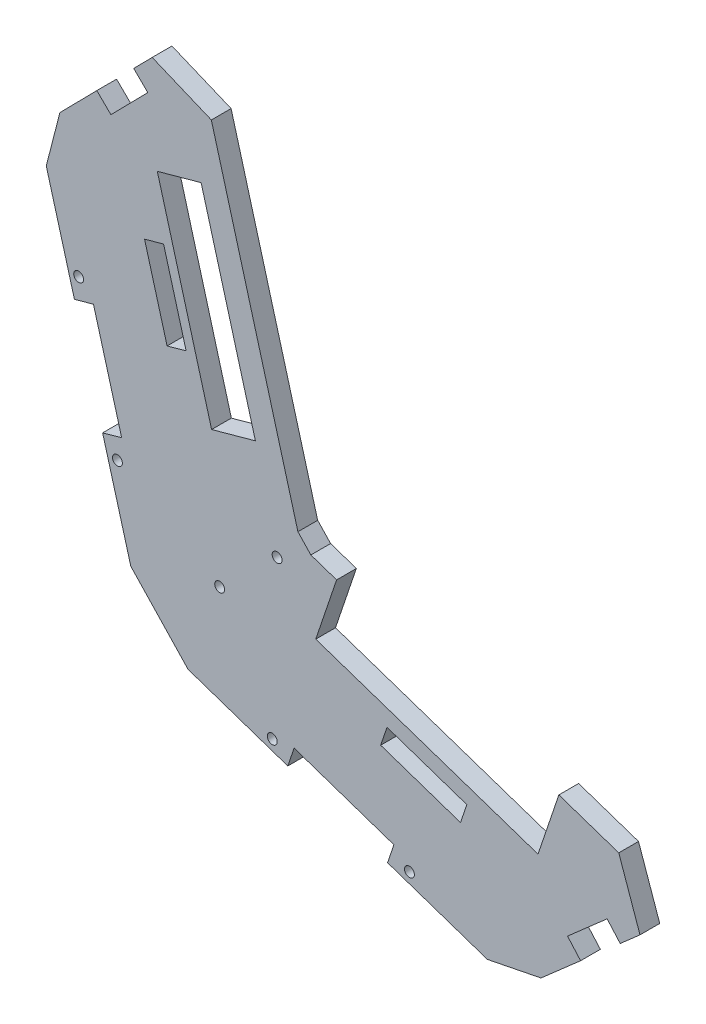
SolidWorks part; units mm, degrees
ref_plane "Alzado" through (0, 0, 0) normal (0, 0, 1) x (1, 0, 0)
ref_plane "Planta" through (0, 0, 0) normal (0, 1, 0) x (1, 0, 0)
ref_plane "Vista lateral" through (0, 0, 0) normal (1, 0, 0) x (0, 0, -1)
sketch "Croquis1" plane through (0, 0, 0) normal (0, 0, 1) x (1, 0, 0)
  line L9 (94.713, -28.6703) -> (124.7846, -2.2941)
  line L10 (124.7846, -2.2941) -> (121.4876, 1.4648)
  line L11 (5.4022, -5.6785) -> (81.1413, -31.3819)
  line L25 (-30.4895, 86.7174) -> (-9.0886, 9.652)
  line L36 (0.9872, 128.6602) -> (-27.0393, 100.1205)
  line L39 (4.5546, 125.1569) -> (0.9872, 128.6602)
  line L40 (-27.0393, 100.1205) -> (-30.4895, 86.7174)
  line L41 (-9.0886, 9.652) -> (5.4022, -5.6785)
  line L42 (81.1413, -31.3819) -> (94.713, -28.6703)
  line L43 (4.5546, 125.1569) -> (29.1628, 36.1106)
  line L44 (29.1628, 36.1106) -> (33.9713, 31.0235)
  line L45 (33.9713, 31.0235) -> (121.4876, 1.4648)
  dimension "D1" = 0.9872
  dimension "D2" = 4.5546
  dimension "D3" = 5.4022
  dimension "D4" = 29.1628
  dimension "D5" = 33.9713
  dimension "D6" = 81.1413
  dimension "D7" = 94.713
  dimension "D8" = 121.4876
  dimension "D9" = 124.7846
  dimension "D10" = 9.0886
  dimension "D11" = 27.0393
  dimension "D12" = 30.4895
  dimension "D13" = 1.4648
  dimension "D14" = 9.652
  dimension "D15" = 31.0235
  dimension "D16" = 36.1106
  dimension "D17" = 86.7174
  dimension "D18" = 100.1205
extrude "Saliente-Extruir1" add sketch "Croquis1" along normal blind 5
sketch "Croquis2" plane through (0, 0, 5) normal (0, 0, 1) x (1, 0, 0)
  line L0 (31.567, 33.5671) -> (-1.8432, 1.9868) construction
  line L1 (33.9713, 31.0235) -> (29.1628, 36.1106) construction
  line L2 (-9.0886, 9.652) -> (5.4022, -5.6785) construction
  circle A0 centre (27.9334, 30.1325) radius 1.25
  circle A1 centre (13.3988, 16.394) radius 1.25
  dimension "D1" = 2.5
  dimension "D2" = 2.5
  dimension "D3" = 20
  dimension "D4" = 5
extrude "Cortar-Extruir1" cut sketch "Croquis2" against normal blind 10
sketch "Croquis3" plane through (0, 0, 0) normal (0, 0, -1) x (-1, 0, 0)
  line L0 (-93.9621, -1.9044) -> (-37.7107, 17.0945)
  line L1 (-121.4876, 1.4648) -> (-33.9713, 31.0235) construction
  line L2 (-93.9621, -1.9044) -> (-97.802, 9.4646)
  line L3 (-37.7107, 17.0945) -> (-41.5506, 28.4636)
  line L4 (-41.5506, 28.4636) -> (-97.802, 9.4646)
  dimension "D1" = 25
  dimension "D2" = 8
  dimension "D3" = 12
extrude "Cortar-Extruir2" cut sketch "Croquis3" against normal blind 10
sketch "Croquis4" plane through (0, 0, 0) normal (0, 0, -1) x (-1, 0, 0)
  line L0 (-11.3559, 49.8643) -> (2.3844, 99.5846)
  line L1 (-29.1628, 36.1106) -> (-4.5546, 125.1569) construction
  line L2 (-11.3559, 49.8643) -> (-22.4404, 52.9276)
  line L3 (-22.4404, 52.9276) -> (-8.7001, 102.6479)
  line L4 (-8.7001, 102.6479) -> (2.3844, 99.5846)
  dimension "D1" = 22.8
  dimension "D2" = 18
  dimension "D3" = 11.5
  dimension "D4" = 2
extrude "Cortar-Extruir3" cut sketch "Croquis4" against normal blind 10
sketch "Croquis5" plane through (0, 0, 0) normal (0, 0, -1) x (-1, 0, 0)
  line L0 (23.3592, 61.0407) -> (18.5415, 62.3786)
  line L1 (30.4895, 86.7174) -> (9.0886, 9.652) construction
  line L2 (18.5415, 62.3786) -> (11.4062, 36.6842)
  line L3 (11.4062, 36.6842) -> (16.2239, 35.3464)
  line L4 (16.2239, 35.3464) -> (23.3592, 61.0407)
  line L5 (-5.4022, -5.6785) -> (-81.1413, -31.3819) construction
  line L6 (-55.8891, -22.8121) -> (-57.496, -18.0773)
  line L7 (-57.496, -18.0773) -> (-32.2438, -9.5076)
  line L8 (-32.2438, -9.5076) -> (-30.637, -14.2424)
  line L9 (-30.637, -14.2424) -> (-55.8891, -22.8121)
  line L11 (-101.4399, -16.1193) -> (-111.4637, -7.3272)
  line L12 (-94.713, -28.6703) -> (-124.7846, -2.2941) construction
  line L13 (-111.4637, -7.3272) -> (-114.7607, -11.0862)
  line L14 (-101.4399, -16.1193) -> (-104.7369, -19.8782)
  line L15 (-104.7369, -19.8782) -> (-114.7607, -11.0862)
  line L16 (-124.7846, -2.2941) -> (-121.4876, 1.4648) construction
  line L17 (14.1297, 106.1304) -> (4.7875, 115.6436)
  line L18 (-0.9872, 128.6602) -> (27.0393, 100.1205) construction
  line L19 (14.1297, 106.1304) -> (17.6972, 109.6337)
  line L20 (4.7875, 115.6436) -> (8.355, 119.1469)
  line L21 (8.355, 119.1469) -> (17.6972, 109.6337)
  dimension "D1" = 26.6667
  dimension "D2" = 26.6667
  dimension "D3" = 5
  dimension "D4" = 26.6667
  dimension "D5" = 26.6667
  dimension "D6" = 5
  dimension "D7" = 13.3333
  dimension "D8" = 13.3333
  dimension "D9" = 5
  dimension "D10" = 13.3333
  dimension "D11" = 13.3333
  dimension "D12" = 5
extrude "Cortar-Extruir4" cut sketch "Croquis5" against normal blind 22
sketch "Croquis6" plane through (0, 0, 0) normal (0, 0, -1) x (-1, 0, 0)
  line L0 (-96.1549, -6.9086) -> (-35.5498, 13.6588)
  line L1 (-35.5498, 13.6588) -> (-33.943, 8.9241)
  line L2 (-33.943, 8.9241) -> (-94.5481, -11.6434)
  line L3 (-94.5481, -11.6434) -> (-96.1549, -6.9086)
  line L4 (-10.6177, 43.3334) -> (6.5069, 104.9998)
  line L5 (6.5069, 104.9998) -> (11.3246, 103.662)
  line L6 (-10.6177, 43.3334) -> (-5.8, 41.9956)
  line L7 (-5.8, 41.9956) -> (11.3246, 103.662)
  line L8 (30.4895, 86.7174) -> (23.3592, 61.0407) construction
  line L9 (-55.8891, -22.8121) -> (-81.1413, -31.3819) construction
  line L10 (-74.3464, -4.7875) -> (-75.9532, -0.0528)
  line L11 (-55.7515, 6.803) -> (-54.1447, 2.0683)
  line L12 (-4.9095, 63.8889) -> (-0.0918, 62.551)
  line L13 (0.7987, 84.4444) -> (5.6164, 83.1065)
  line L14 (-30.637, -14.2424) -> (-32.2438, -9.5076) construction
  line L15 (11.4062, 36.6842) -> (16.2239, 35.3464) construction
  dimension "D1" = 5
  dimension "D2" = 5
  dimension "D3" = 23
  dimension "D4" = 23
  dimension "D5" = 64
  dimension "D6" = 64
  dimension "D7" = 21.3333
  dimension "D8" = 21.3333
  dimension "D9" = 21.3333
  dimension "D10" = 21.3333
  dimension "D11" = 17.019
  dimension "D12" = 21.8471
extrude "Cortar-Extruir5" cut sketch "Croquis6" against normal blind 10 contours L11 L0 L10 L2 | L13 L4 L12 L7
sketch "Croquis10" plane through (0, 0, 0) normal (0, 0, -1) x (-1, 0, 0)
  line L0 (-121.4876, 1.4648) -> (-97.802, 9.4646) construction
  line L1 (-121.4876, 1.4648) -> (-97.802, 9.4646)
  line L2 (-29.1628, 36.1106) -> (-4.5546, 125.1569) construction
  line L3 (-33.9713, 31.0235) -> (-29.1628, 36.1106) construction
  line L4 (-41.5506, 28.4636) -> (-33.9713, 31.0235) construction
  line L5 (-29.1628, 36.1106) -> (-4.5546, 125.1569)
  line L6 (-33.9713, 31.0235) -> (-29.1628, 36.1106)
  line L7 (-41.5506, 28.4636) -> (-33.9713, 31.0235)
  line L8 (-122.9275, 5.7282) -> (-99.242, 13.728)
  line L9 (-42.9906, 32.727) -> (-36.4722, 34.9286)
  line L10 (-36.4722, 34.9286) -> (-33.202, 38.3883)
  line L11 (-33.202, 38.3883) -> (-8.8921, 126.3555)
  line L12 (-122.9275, 5.7282) -> (-121.4876, 1.4648)
  line L13 (-99.242, 13.728) -> (-97.802, 9.4646)
  line L14 (-42.9906, 32.727) -> (-41.5506, 28.4636)
  line L15 (-4.5546, 125.1569) -> (-8.8921, 126.3555)
  dimension "D1" = 4.5
  dimension "D2" = 4.5
extrude "Saliente-Extruir3" add sketch "Croquis10" against normal blind 5 contours L13 L1 L12 L8 | L15 L11 L10 L9 L14 L7 L6 L5
sketch "Croquis11" plane through (0, 0, 0) normal (0, 0, -1) x (-1, 0, 0)
  line L0 (-119.7726, -6.6901) -> (-114.4007, 8.6082)
  line L1 (-114.7607, -11.0862) -> (-124.7846, -2.2941) construction
  line L2 (-122.9275, 5.7282) -> (-99.242, 13.728) construction
  line L3 (3.6839, 123.9036) -> (-11.2894, 117.6807)
  line L4 (-0.9872, 128.6602) -> (8.355, 119.1469) construction
  line L5 (-33.202, 38.3883) -> (-8.8921, 126.3555) construction
  line L6 (-124.7846, -2.2941) -> (-121.4876, 1.4648) construction
  line L7 (-122.9275, 5.7282) -> (-121.4876, 1.4648) construction
  line L8 (-119.7726, -6.6901) -> (-124.7846, -2.2941)
  line L9 (-124.7846, -2.2941) -> (-121.4876, 1.4648)
  line L10 (-122.9275, 5.7282) -> (-121.4876, 1.4648)
  line L11 (-122.9275, 5.7282) -> (-114.4007, 8.6082)
  line L12 (-4.5546, 125.1569) -> (-8.8921, 126.3555) construction
  line L13 (-4.5546, 125.1569) -> (-8.8921, 126.3555)
  line L14 (-4.5546, 125.1569) -> (-0.9872, 128.6602) construction
  line L15 (-11.2894, 117.6807) -> (-8.8921, 126.3555)
  line L16 (-4.5546, 125.1569) -> (-0.9872, 128.6602)
  line L17 (-0.9872, 128.6602) -> (3.6839, 123.9036)
  dimension "D1" = 9
  dimension "D2" = 9
extrude "Cortar-Extruir7" cut sketch "Croquis11" against normal blind 5 contours L10 L9 L8 L0 L11 | L15 L13 L16 L17 L3
sketch "Croquis7" plane through (0, 0, 0) normal (0, 0, -1) x (-1, 0, 0)
  line L0 (-99.242, 13.728) -> (-93.9621, -1.9044) construction
  line L17 (-9.374, 126.4887) -> (-4.5546, 125.1569)
  line L18 (-123.0875, 6.2019) -> (-93.7175, 16.1217)
  line L19 (-43.1506, 33.2007) -> (-36.7501, 35.3624)
  line L20 (-33.6508, 38.6413) -> (-9.374, 126.4887)
  line L21 (-36.7501, 35.3624) -> (-33.6508, 38.6413)
  line L22 (-43.1506, 33.2007) -> (-36.7501, 35.3624)
  line L23 (-33.6508, 38.6413) -> (-9.374, 126.4887)
  line L24 (-36.7501, 35.3624) -> (-33.6508, 38.6413)
  line L25 (-123.0875, 6.2019) -> (-99.3452, 14.2209)
  line L26 (-123.0875, 6.2019) -> (-121.4876, 1.4648)
  line L27 (-121.4876, 1.4648) -> (-97.7452, 9.4838)
  line L28 (-33.9713, 31.0235) -> (-29.1628, 36.1106)
  line L29 (-29.1628, 36.1106) -> (-4.5546, 125.1569)
  line L30 (-97.7452, 9.4838) -> (-99.3452, 14.2209)
  line L31 (-41.5506, 28.4636) -> (-43.1506, 33.2007)
  line L32 (-41.5506, 28.4636) -> (-33.9713, 31.0235)
  dimension "D1" = 5
  dimension "D2" = 5
extrude "Saliente-Extruir2" [suppressed] add sketch "Croquis7" against normal blind 5
sketch "Croquis8" plane through (0, 0, 0) normal (0, 0, -1) x (-1, 0, 0)
  line L0 (2.3844, 99.5846) -> (-8.7001, 102.6479) construction
  line L1 (-22.4404, 52.9276) -> (-11.3559, 49.8643) construction
  line L2 (-8.7001, 102.6479) -> (-22.4404, 52.9276) construction
  line L3 (-11.3559, 49.8643) -> (2.3844, 99.5846) construction
  line L4 (0.7987, 84.4444) -> (5.6164, 83.1065) construction
  line L5 (-4.9095, 63.8889) -> (0.7987, 84.4444) construction
  line L6 (-0.0918, 62.551) -> (5.6164, 83.1065) construction
  line L7 (-4.9095, 63.8889) -> (-0.0918, 62.551) construction
  line L8 (-54.1447, 2.0683) -> (-74.3464, -4.7875) construction
  line L9 (-74.3464, -4.7875) -> (-75.9532, -0.0528) construction
  line L10 (-55.7515, 6.803) -> (-54.1447, 2.0683) construction
  line L11 (-75.9532, -0.0528) -> (-55.7515, 6.803) construction
  line L12 (2.3844, 99.5846) -> (-8.7001, 102.6479)
  line L13 (-22.4404, 52.9276) -> (-11.3559, 49.8643)
  line L14 (-8.7001, 102.6479) -> (-22.4404, 52.9276)
  line L15 (-11.3559, 49.8643) -> (2.3844, 99.5846)
  line L16 (0.7987, 84.4444) -> (5.6164, 83.1065)
  line L17 (-4.9095, 63.8889) -> (0.7987, 84.4444)
  line L18 (-0.0918, 62.551) -> (5.6164, 83.1065)
  line L19 (-4.9095, 63.8889) -> (-0.0918, 62.551)
  line L20 (-54.1447, 2.0683) -> (-74.3464, -4.7875)
  line L21 (-74.3464, -4.7875) -> (-75.9532, -0.0528)
  line L22 (-55.7515, 6.803) -> (-54.1447, 2.0683)
  line L23 (-75.9532, -0.0528) -> (-55.7515, 6.803)
  line L34 (17.6972, 109.6337) -> (14.1297, 106.1304)
  line L35 (14.1297, 106.1304) -> (4.7875, 115.6436)
  line L36 (4.7875, 115.6436) -> (8.355, 119.1469)
  line L37 (8.355, 119.1469) -> (3.6839, 123.9036)
  line L38 (3.6839, 123.9036) -> (-11.2894, 117.6807)
  line L39 (-11.2894, 117.6807) -> (-33.202, 38.3883)
  line L40 (-11.2894, 117.6807) -> (-33.202, 38.3883)
  line L41 (-33.202, 38.3883) -> (-36.4722, 34.9286)
  line L42 (-33.202, 38.3883) -> (-36.4722, 34.9286)
  line L43 (-36.4722, 34.9286) -> (-42.9906, 32.727)
  line L44 (-37.7107, 17.0945) -> (-93.9621, -1.9044)
  line L45 (-36.4722, 34.9286) -> (-42.9906, 32.727)
  line L46 (-42.9906, 32.727) -> (-37.7107, 17.0945)
  line L47 (-42.9906, 32.727) -> (-37.7107, 17.0945)
  line L48 (3.6839, 123.9036) -> (-11.2894, 117.6807)
  line L49 (-119.7726, -6.6901) -> (-114.7607, -11.0862)
  line L50 (-114.7607, -11.0862) -> (-111.4637, -7.3272)
  line L51 (-111.4637, -7.3272) -> (-101.4399, -16.1193)
  line L52 (-101.4399, -16.1193) -> (-104.7369, -19.8782)
  line L53 (-104.7369, -19.8782) -> (-94.713, -28.6703)
  line L54 (-94.713, -28.6703) -> (-81.1413, -31.3819)
  line L55 (-81.1413, -31.3819) -> (-55.8891, -22.8121)
  line L56 (-55.8891, -22.8121) -> (-57.496, -18.0773)
  line L57 (-57.496, -18.0773) -> (-32.2438, -9.5076)
  line L58 (-32.2438, -9.5076) -> (-30.637, -14.2424)
  line L59 (-30.637, -14.2424) -> (-5.4022, -5.6785)
  line L60 (-5.4022, -5.6785) -> (9.0886, 9.652)
  line L61 (9.0886, 9.652) -> (16.2239, 35.3464)
  line L62 (16.2239, 35.3464) -> (11.4062, 36.6842)
  line L63 (11.4062, 36.6842) -> (18.5415, 62.3786)
  line L64 (18.5415, 62.3786) -> (23.3592, 61.0407)
  line L65 (23.3592, 61.0407) -> (30.4895, 86.7174)
  line L66 (30.4895, 86.7174) -> (27.0393, 100.1205)
  line L67 (27.0393, 100.1205) -> (17.6972, 109.6337)
  line L68 (17.6972, 109.6337) -> (14.1297, 106.1304)
  line L69 (14.1297, 106.1304) -> (4.7875, 115.6436)
  line L70 (4.7875, 115.6436) -> (8.355, 119.1469)
  line L71 (8.355, 119.1469) -> (3.6839, 123.9036)
  line L78 (-37.7107, 17.0945) -> (-93.9621, -1.9044)
  line L83 (-119.7726, -6.6901) -> (-114.7607, -11.0862)
  line L84 (-114.7607, -11.0862) -> (-111.4637, -7.3272)
  line L85 (-111.4637, -7.3272) -> (-101.4399, -16.1193)
  line L86 (-101.4399, -16.1193) -> (-104.7369, -19.8782)
  line L87 (-104.7369, -19.8782) -> (-94.713, -28.6703)
  line L88 (-94.713, -28.6703) -> (-81.1413, -31.3819)
  line L89 (-81.1413, -31.3819) -> (-55.8891, -22.8121)
  line L90 (-55.8891, -22.8121) -> (-57.496, -18.0773)
  line L91 (-57.496, -18.0773) -> (-32.2438, -9.5076)
  line L92 (-32.2438, -9.5076) -> (-30.637, -14.2424)
  line L93 (-30.637, -14.2424) -> (-5.4022, -5.6785)
  line L94 (-5.4022, -5.6785) -> (9.0886, 9.652)
  line L95 (9.0886, 9.652) -> (16.2239, 35.3464)
  line L96 (16.2239, 35.3464) -> (11.4062, 36.6842)
  line L97 (11.4062, 36.6842) -> (18.5415, 62.3786)
  line L98 (18.5415, 62.3786) -> (23.3592, 61.0407)
  line L99 (23.3592, 61.0407) -> (30.4895, 86.7174)
  line L100 (30.4895, 86.7174) -> (27.0393, 100.1205)
  line L101 (27.0393, 100.1205) -> (17.6972, 109.6337)
  line L124 (-99.242, 13.728) -> (-114.4007, 8.6082)
  line L125 (-99.242, 13.728) -> (-114.4007, 8.6082)
  line L132 (-93.9621, -1.9044) -> (-99.242, 13.728)
  line L133 (-93.9621, -1.9044) -> (-99.242, 13.728)
  line L138 (-114.4007, 8.6082) -> (-119.7726, -6.6901)
  line L139 (-114.4007, 8.6082) -> (-119.7726, -6.6901)
  circle A0 centre (-13.3988, 16.394) radius 1.25 construction
  circle A1 centre (-27.9334, 30.1325) radius 1.25 construction
  circle A2 centre (-13.3988, 16.394) radius 1.25
  circle A3 centre (-27.9334, 30.1325) radius 1.25
  dimension "D1" = 0
sketch "Croquis9" plane through (0, 0, 0) normal (0, 0, -1) x (-1, 0, 0)
  line L0 (-57.496, -18.0773) -> (-55.8891, -22.8121) construction
  line L1 (-55.8891, -22.8121) -> (-81.1413, -31.3819) construction
  line L2 (-5.4022, -5.6785) -> (-30.637, -14.2424) construction
  line L3 (-30.637, -14.2424) -> (-32.2438, -9.5076) construction
  line L4 (11.4062, 36.6842) -> (16.2239, 35.3464) construction
  line L5 (16.2239, 35.3464) -> (9.0886, 9.652) construction
  line L6 (30.4895, 86.7174) -> (23.3592, 61.0407) construction
  line L7 (23.3592, 61.0407) -> (18.5415, 62.3786) construction
  circle A0 centre (-26.7056, -10.2681) radius 1.25
  circle A1 centre (-61.4273, -22.0516) radius 1.25
  circle A2 centre (12.4772, 31.1976) radius 1.25
  circle A3 centre (22.2882, 66.5273) radius 1.25
  dimension "D1" = 2.5
  dimension "D2" = 2.5
  dimension "D3" = 2.5
  dimension "D4" = 2.5
  dimension "D5" = 5
  dimension "D6" = 2.5
  dimension "D7" = 2.5
  dimension "D8" = 5
  dimension "D9" = 5
  dimension "D10" = 2.5
  dimension "D11" = 2.5
  dimension "D12" = 5
extrude "Cortar-Extruir6" cut sketch "Croquis9" against normal blind 10
